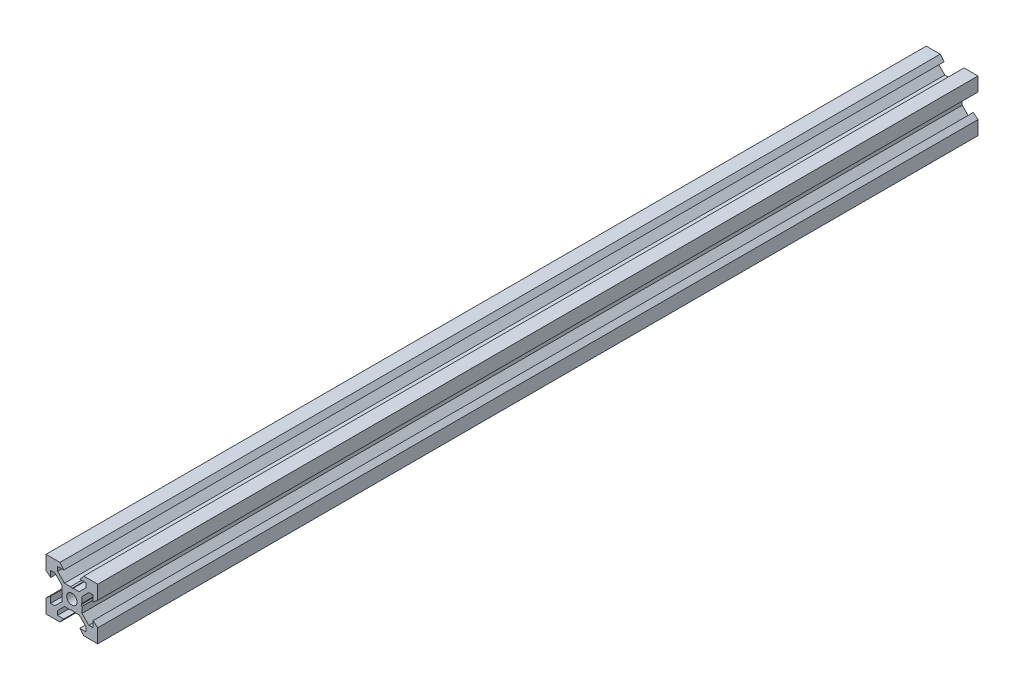
SolidWorks part; units mm, degrees
ref_plane "Front Plane" through (0, 0, 0) normal (0, 0, 1) x (1, 0, 0)
ref_plane "Top Plane" through (0, 0, 0) normal (0, 1, 0) x (1, 0, 0)
ref_plane "Right Plane" through (0, 0, 0) normal (1, 0, 0) x (0, 0, -1)
sketch "Sketch1" plane through (0, 0, 0) normal (0, 0, 1) x (1, 0, 0)
  line L0 (10, 10) -> (4.6104, 10) construction
  line L1 (10, 10) -> (10, 4.6104) construction
  line L2 (10, -10) -> (10, -4.6104) construction
  line L3 (10, -10) -> (4.6104, -10) construction
  line L4 (10, 10) -> (10, 4.6104)
  line L5 (6.5607, 5.5) -> (8.2, 5.5)
  line L6 (5.5, 8.2) -> (5.5, 6.5607)
  line L7 (10, 10) -> (4.6104, 10)
  line L8 (10, 10) -> (10, 4.6104)
  line L9 (6.5607, 5.5) -> (3.9, 2.8393)
  line L10 (5.5, 6.5607) -> (2.8393, 3.9)
  line L11 (10, 4.6104) -> (8.2, 3.1)
  line L12 (4.6104, 10) -> (3.1, 8.2)
  line L13 (8.2, 3.1) -> (8.2, 5.5)
  line L14 (3.1, 8.2) -> (5.5, 8.2)
  line L15 (-6.5607, 5.5) -> (-8.2, 5.5)
  line L16 (6.5607, -5.5) -> (8.2, -5.5)
  line L17 (3.1, -8.2) -> (5.5, -8.2)
  line L18 (8.2, -3.1) -> (8.2, -5.5)
  line L19 (4.6104, -10) -> (3.1, -8.2)
  line L20 (10, -4.6104) -> (8.2, -3.1)
  line L21 (0.5196, -3.9) -> (0, -3.6)
  line L22 (0.5196, 3.9) -> (0, 3.6)
  line L23 (3.6, 0) -> (3.9, -0.5196)
  line L24 (3.9, 0.5196) -> (3.6, 0)
  line L25 (3.9, 0.5196) -> (3.9, 2.8393)
  line L26 (2.8393, 3.9) -> (0.5196, 3.9)
  line L27 (3.9, -2.8393) -> (3.9, -0.5196)
  line L28 (2.8393, -3.9) -> (0.5196, -3.9)
  line L29 (5.5, -6.5607) -> (2.8393, -3.9)
  line L30 (6.5607, -5.5) -> (3.9, -2.8393)
  line L31 (10, -10) -> (10, -4.6104)
  line L32 (10, -10) -> (4.6104, -10)
  line L33 (5.5, -8.2) -> (5.5, -6.5607)
  line L34 (-6.5607, -5.5) -> (-8.2, -5.5)
  line L35 (10, -10) -> (10, -4.6104)
  line L36 (0, 0) -> (0, 8.2) construction
  line L37 (-10, -10) -> (-4.6104, -10) construction
  line L38 (-10, -10) -> (-10, -4.6104) construction
  line L39 (-10, 10) -> (-10, 4.6104) construction
  line L40 (-10, 10) -> (-4.6104, 10) construction
  line L41 (-10, -10) -> (-10, -4.6104)
  line L43 (-5.5, -8.2) -> (-5.5, -6.5607)
  line L44 (-10, -10) -> (-4.6104, -10)
  line L45 (-10, -10) -> (-10, -4.6104)
  line L46 (-6.5607, -5.5) -> (-3.9, -2.8393)
  line L47 (-5.5, -6.5607) -> (-2.8393, -3.9)
  line L48 (-2.8393, -3.9) -> (-0.5196, -3.9)
  line L49 (-3.9, -2.8393) -> (-3.9, -0.5196)
  line L50 (-2.8393, 3.9) -> (-0.5196, 3.9)
  line L51 (-3.9, 0.5196) -> (-3.9, 2.8393)
  line L52 (-3.9, 0.5196) -> (-3.6, 0)
  line L53 (-3.6, 0) -> (-3.9, -0.5196)
  line L54 (-0.5196, 3.9) -> (0, 3.6)
  line L55 (-0.5196, -3.9) -> (0, -3.6)
  line L56 (-10, -4.6104) -> (-8.2, -3.1)
  line L57 (-4.6104, -10) -> (-3.1, -8.2)
  line L58 (-8.2, -3.1) -> (-8.2, -5.5)
  line L59 (-3.1, -8.2) -> (-5.5, -8.2)
  line L60 (-10, -10) -> (10, -10) construction
  line L61 (-10, -10) -> (-10, 10) construction
  line L62 (-3.1, 8.2) -> (-5.5, 8.2)
  line L63 (-8.2, 3.1) -> (-8.2, 5.5)
  line L64 (-4.6104, 10) -> (-3.1, 8.2)
  line L65 (-10, 4.6104) -> (-8.2, 3.1)
  line L66 (-5.5, 6.5607) -> (-2.8393, 3.9)
  line L67 (-6.5607, 5.5) -> (-3.9, 2.8393)
  line L68 (-10, 10) -> (-10, 4.6104)
  line L69 (-10, 10) -> (-4.6104, 10)
  line L70 (-5.5, 8.2) -> (-5.5, 6.5607)
  line L71 (-10, 10) -> (10, 10) construction
  line L72 (-10, 10) -> (-10, 4.6104)
  line L73 (10, -10) -> (10, 10) construction
  line L74 (-10, -10) -> (10, 10) construction
  line L75 (-10, 10) -> (10, -10) construction
  circle A0 centre (0, 0) radius 2
  dimension "D7" = 4
  dimension "D1" = 20
  dimension "D2" = 5.3896
  dimension "D3" = 4.5
  dimension "D4" = 50
  dimension "D5" = 1.8
  dimension "D6" = 1.5104
  dimension "D8" = 5.5
  dimension "D9" = 120
  dimension "D10" = 0.3
  dimension "D11" = 2.3197
  dimension "D12" = 7.8
  dimension "D13" = 7.8
  dimension "D14" = 1.5
  dimension "D15" = 2.6607
extrude "Boss-Extrude1" add sketch "Sketch1" along normal mid plane 340.33 contours L70 L62 L64 L69 L68 L65 L63 L15 L67 L51 L52 L53 L49 L46 L34 L58 L56 L41 L44 L57 L59 L43 L47 L48 L55 L21 L28 L29 L33 L17 L19 L32 L31 L20 L18 L16 L30 L27 L23 L24 L25 L9 L5 L13 L11 L4 L7 L12 L14 L6 L10
